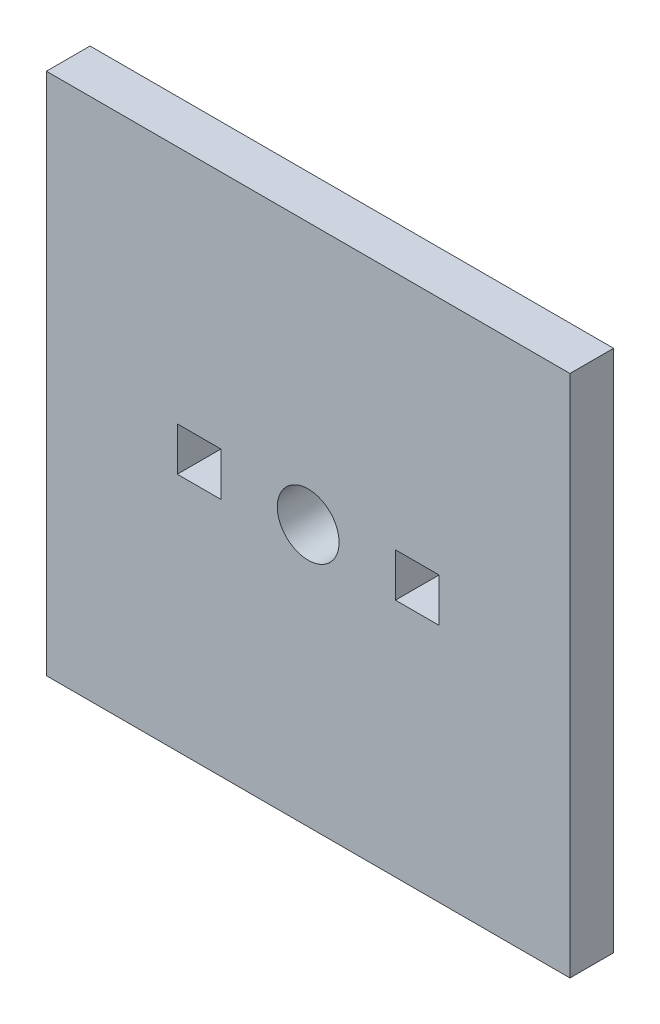
SolidWorks part; units mm, degrees
ref_plane "Front Plane" through (0, 0, 0) normal (0, 0, 1) x (1, 0, 0)
ref_plane "Top Plane" through (0, 0, 0) normal (0, 1, 0) x (1, 0, 0)
ref_plane "Right Plane" through (0, 0, 0) normal (1, 0, 0) x (0, 0, -1)
sketch "Sketch1" plane through (0, 0, 0) normal (0, 0, 1) x (1, 0, 0)
  line L1 (-19.05, 19.05) -> (19.05, 19.05)
  line L2 (-19.05, 19.05) -> (-19.05, -19.05)
  line L3 (-19.05, -19.05) -> (19.05, -19.05)
  line L4 (19.05, 19.05) -> (19.05, -19.05)
  line L5 (-19.05, 19.05) -> (19.05, -19.05) construction
  line L6 (-19.05, -19.05) -> (19.05, 19.05) construction
  point P0 (0, 0)
  dimension "D1" = 38.1
  dimension "D2" = 38.1
extrude "Boss-Extrude1" add sketch "Sketch1" along normal blind 3.175
hole_wizard "#8 Clearance Hole1" positions "Sketch3" profile "Sketch2" hole size "#8" standard "ANSI Inch"
sketch "Sketch3" plane through (0, 0, 3.175) normal (0, 0, 1) x (1, 0, 0)
  point P0 (0, 0)
sketch "Sketch2" plane through (0, 0, 3.175) normal (1, 0, 0) x (0, -1, 0)
  line L0 (0, 0) -> (0, 11.5107)
  line L1 (0, 11.5107) -> (2.2479, 10.16)
  line L2 (2.2479, 10.16) -> (2.2479, 0)
  line L5 (2.2479, 0) -> (0, 0)
  line L10 (0, 11.5107) -> (-2.2479, 10.16) construction
  line L11 (0, -6.35) -> (0, 107.95) construction
  dimension "Hole Dia." = 4.4958
  dimension "Hole Depth" = 10.16
  dimension "Drill Angle" = 118
sketch "Sketch4" plane through (0, 0, 3.175) normal (0, 0, 1) x (1, 0, 0)
  line L1 (-9.525, 1.5875) -> (-6.35, 1.5875)
  line L2 (-9.525, 1.5875) -> (-9.525, -1.5875)
  line L3 (-9.525, -1.5875) -> (-6.35, -1.5875)
  line L4 (-6.35, 1.5875) -> (-6.35, -1.5875)
  line L5 (-9.525, 1.5875) -> (-6.35, -1.5875) construction
  line L6 (-9.525, -1.5875) -> (-6.35, 1.5875) construction
  line L7 (6.35, 1.5875) -> (9.525, 1.5875)
  line L8 (6.35, 1.5875) -> (6.35, -1.5875)
  line L9 (6.35, -1.5875) -> (9.525, -1.5875)
  line L10 (9.525, 1.5875) -> (9.525, -1.5875)
  line L11 (6.35, 1.5875) -> (9.525, -1.5875) construction
  line L12 (6.35, -1.5875) -> (9.525, 1.5875) construction
  point P0 (-7.9375, 0)
  point P5 (7.9375, 0)
  dimension "D1" = 3.175
  dimension "D2" = 3.175
  dimension "D3" = 3.175
  dimension "D4" = 3.175
  dimension "D5" = 6.35
  dimension "D6" = 6.35
extrude "Cut-Extrude1" cut sketch "Sketch4" against normal blind 3.175
